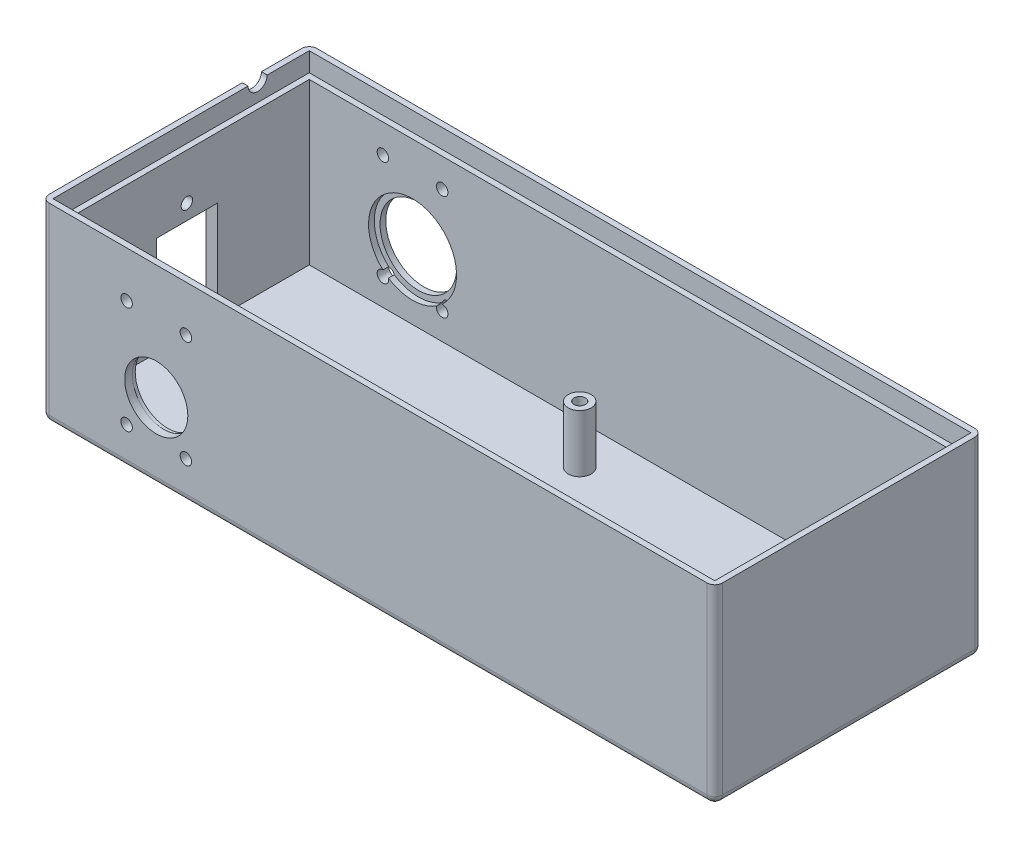
SolidWorks part; units mm, degrees
ref_plane "Front Plane" through (0, 0, 0) normal (0, 0, 1) x (1, 0, 0)
ref_plane "Top Plane" through (0, 0, 0) normal (0, 1, 0) x (1, 0, 0)
ref_plane "Right Plane" through (0, 0, 0) normal (1, 0, 0) x (0, 0, -1)
sketch "Sketch1" plane through (0, 0, 0) normal (0, 1, 0) x (1, 0, 0)
  line L1 (88, -35) -> (-88, -35)
  line L2 (88, -35) -> (88, 35)
  line L3 (88, 35) -> (-88, 35)
  line L4 (-88, -35) -> (-88, 35)
  line L5 (88, -35) -> (-88, 35) construction
  line L6 (88, 35) -> (-88, -35) construction
  point P0 (0, 0)
  dimension "D1" = 176
  dimension "D2" = 70
extrude "Boss-Extrude1" add sketch "Sketch1" along normal blind 50
sketch "Sketch2" plane through (0, 50, 0) normal (0, 1, 0) x (1, 0, 0)
  line L0 (-88, 35) -> (-88, -35) construction
  line L1 (85, -32) -> (-85, -32)
  line L2 (85, -32) -> (85, 32)
  line L3 (85, 32) -> (-85, 32)
  line L4 (-85, -32) -> (-85, 32)
  line L5 (85, -32) -> (-85, 32) construction
  line L6 (85, 32) -> (-85, -32) construction
  line L7 (88, 35) -> (-88, 35) construction
  point P0 (0, 0)
  dimension "D1" = 3
  dimension "D2" = 3
extrude "Cut-Extrude1" cut sketch "Sketch2" against normal blind 47
sketch "Sketch3" plane through (0, 50, 0) normal (0, 1, 0) x (1, 0, 0)
  line L0 (-88, 35) -> (-88, -35) construction
  line L1 (86.5, -33.5) -> (-86.5, -33.5)
  line L2 (86.5, -33.5) -> (86.5, 33.5)
  line L3 (86.5, 33.5) -> (-86.5, 33.5)
  line L4 (-86.5, -33.5) -> (-86.5, 33.5)
  line L5 (86.5, -33.5) -> (-86.5, 33.5) construction
  line L6 (86.5, 33.5) -> (-86.5, -33.5) construction
  line L7 (88, 35) -> (-88, 35) construction
  point P0 (0, 0)
  dimension "D1" = 1.5
  dimension "D2" = 1.5
extrude "Cut-Extrude2" cut sketch "Sketch3" against normal blind 5
sketch "Sketch4" plane through (0, 3, 0) normal (0, 1, 0) x (1, 0, 0)
  line L0 (85, -32) -> (85, 32) construction
  line L1 (-85, -32) -> (85, -32) construction
  line L3 (-3.8, 21.5) -> (71.2, 21.5) construction
  circle A0 centre (-4.8, -27) radius 3
  circle A1 centre (78, -27) radius 3
  circle A2 centre (71.2, 21.5) radius 3
  circle A3 centre (-3.8, 21.5) radius 3
  circle A4 centre (-4.8, -27) radius 1.5
  circle A5 centre (-3.8, 21.5) radius 1.5
  circle A6 centre (71.2, 21.5) radius 1.5
  circle A7 centre (78, -27) radius 1.5
  dimension "D1" = 6
  dimension "D7" = 3
  dimension "D2" = 82.8
  dimension "D3" = 48.5
  dimension "D4" = 75
  dimension "D5" = 7
  dimension "D6" = 5
  dimension "D8" = 1
extrude "Boss-Extrude2" add sketch "Sketch4" along normal blind 15
sketch "Sketch5" plane through (0, 0, -35) normal (0, 0, -1) x (-1, 0, 0)
  line L0 (-88, 0) -> (88, 0) construction
  line L1 (88, 50) -> (88, 0) construction
  line L2 (58, 20) -> (58, 59.0899) construction
  circle A0 centre (58, 20) radius 10
  circle A1 centre (65.75, 37.5) radius 1.5
  circle A2 centre (50.25, 37.5) radius 1.5
  circle A3 centre (50.25, 10) radius 1.5
  circle A4 centre (65.75, 10) radius 1.5
  dimension "D1" = 20
  dimension "D4" = 3
  dimension "D2" = 20
  dimension "D3" = 30
  dimension "D5" = 15.5
  dimension "D6" = 27.5
  dimension "D7" = 10
extrude "Cut-Extrude3" cut sketch "Sketch5" against normal up to next
sketch "Sketch6" plane through (0, 0, -32) normal (0, 0, 1) x (1, 0, 0)
  circle A0 centre (-58, 20) radius 11.5
  circle A1 centre (-58, 20) radius 10 construction
  dimension "D1" = 1.5
extrude "Cut-Extrude4" cut sketch "Sketch6" against normal blind 1.5
sketch "Sketch7" plane through (0, 0, 35) normal (0, 0, 1) x (1, 0, 0)
  line L0 (-88, 0) -> (88, 0) construction
  line L1 (-88, 50) -> (-88, 0) construction
  line L2 (-58, 20) -> (-58, 52.5143) construction
  circle A0 centre (-58, 20) radius 8.25
  circle A1 centre (-65.75, 38) radius 1.5
  circle A2 centre (-50.25, 38) radius 1.5
  circle A3 centre (-65.75, 10) radius 1.5
  circle A4 centre (-50.25, 10) radius 1.5
  dimension "D1" = 16.5
  dimension "D4" = 3
  dimension "D2" = 20
  dimension "D3" = 30
  dimension "D5" = 10
  dimension "D6" = 15.5
  dimension "D7" = 28
extrude "Cut-Extrude5" cut sketch "Sketch7" against normal up to next
sketch "Sketch8" plane through (0, 0, 32) normal (0, 0, -1) x (-1, 0, 0)
  circle A0 centre (58, 20) radius 8.5
  dimension "D1" = 17
extrude "Cut-Extrude6" cut sketch "Sketch8" against normal blind 1
fillet "Fillet1" radius 2 8 edges at (0, 0, 35) (-88, 25, 35) (-88, 0, 0) (-88, 25, -35) (88, 25, 35) (88, 0, 0) (0, 0, -35) (88, 25, -35)
sketch "Sketch9" plane through (-88, 0, 0) normal (-1, 0, 0) x (0, 0, 1)
  line L0 (-33, 2) -> (33, 2) construction
  line L1 (8, 8) -> (-8, 8)
  line L2 (8, 8) -> (8, 29)
  line L3 (8, 29) -> (-8, 29)
  line L4 (-8, 8) -> (-8, 29)
  line L5 (8, 8) -> (-8, 29) construction
  line L6 (8, 29) -> (-8, 8) construction
  circle A0 centre (0, 33) radius 1.5
  circle A1 centre (0, 6) radius 1
  point P0 (0, 18.5)
  dimension "D3" = 3
  dimension "D4" = 2
  dimension "D1" = 21
  dimension "D2" = 16
  dimension "D5" = 4
  dimension "D6" = 2
  dimension "D7" = 6
extrude "Cut-Extrude7" cut sketch "Sketch9" against normal up to next
sketch "Sketch10" plane through (-88, 0, 0) normal (-1, 0, 0) x (0, 0, 1)
  line L0 (-33, 50) -> (33, 50) construction
  line L1 (-35, 2) -> (-35, 50) construction
  circle A0 centre (-20, 50) radius 2.5
  dimension "D1" = 5
  dimension "D2" = 15
extrude "Cut-Extrude8" cut sketch "Sketch10" against normal up to next
